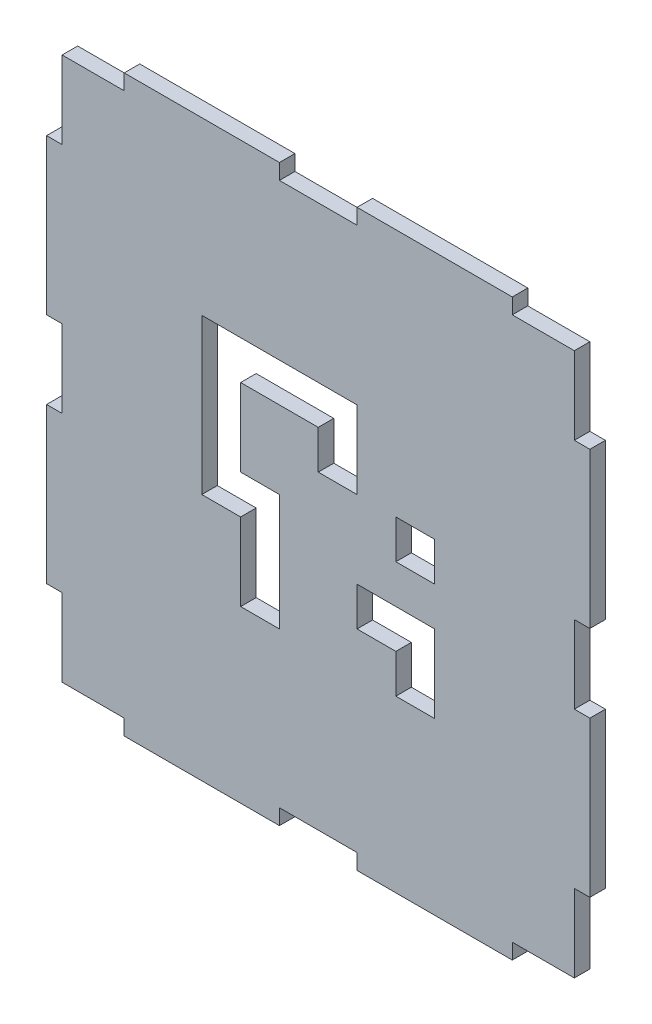
SolidWorks part; units mm, degrees
ref_plane "Front Plane" through (0, 0, 0) normal (0, 0, 1) x (1, 0, 0)
ref_plane "Top Plane" through (0, 0, 0) normal (0, 1, 0) x (1, 0, 0)
ref_plane "Right Plane" through (0, 0, 0) normal (1, 0, 0) x (0, 0, -1)
sketch "Sketch1" plane through (0, 0, 0) normal (0, 0, 1) x (1, 0, 0)
  line L1 (-33, -35) -> (33, -35)
  line L2 (-33, -35) -> (-33, 35)
  line L3 (-33, 35) -> (33, 35)
  line L4 (33, -35) -> (33, 35)
  line L5 (0, 35) -> (0, -35) construction
  line L6 (-33, 0) -> (33, 0) construction
  point P0 (0, 0)
  dimension "D1" = 66
  dimension "D2" = 70
extrude "Boss-Extrude1" add sketch "Sketch1" along normal blind 2
sketch "Sketch2" plane through (0, 0, 0) normal (0, 0, -1) x (-1, 0, 0)
  line L0 (-33, -35) -> (-33, 35) construction
  line L1 (-31, 5) -> (-35, 5)
  line L2 (-31, 5) -> (-31, -5)
  line L3 (-31, -5) -> (-35, -5)
  line L4 (-35, 5) -> (-35, -5)
  line L5 (-33, -5) -> (-33, 5) construction
  line L6 (-31, 0) -> (-35, 0) construction
  line L7 (-33, -35) -> (-33, 0)
  line L8 (-33, -5) -> (-35, -5)
  line L9 (-33, -5) -> (-33, -25)
  line L10 (-33, -25) -> (-35, -25)
  line L11 (-35, -5) -> (-35, -25)
  line L12 (-33, 5) -> (-35, 5)
  line L13 (-33, 5) -> (-33, 25)
  line L14 (-33, 25) -> (-35, 25)
  line L15 (-35, 5) -> (-35, 25)
  line L16 (35, 5) -> (31, 5)
  line L17 (35, 5) -> (35, -5)
  line L18 (35, -5) -> (31, -5)
  line L19 (31, 5) -> (31, -5)
  line L20 (33, -5) -> (33, 5) construction
  line L21 (35, 0) -> (31, 0) construction
  line L22 (33, -35) -> (33, 0)
  line L23 (33, -5) -> (31, -5)
  line L24 (33, -5) -> (33, -25)
  line L25 (33, -25) -> (31, -25)
  line L26 (31, -5) -> (31, -25)
  line L27 (33, 5) -> (31, 5)
  line L28 (33, 5) -> (33, 25)
  line L29 (33, 25) -> (31, 25)
  line L30 (31, 5) -> (31, 25)
  line L32 (33, -5) -> (35, -5)
  line L33 (33, -5) -> (33, -25)
  line L34 (33, -25) -> (35, -25)
  line L35 (35, -5) -> (35, -25)
  line L36 (35, 5) -> (33, 5)
  line L37 (35, 5) -> (35, 25)
  line L38 (35, 25) -> (33, 25)
  line L39 (33, 5) -> (33, 25)
  point P0 (-33, 0)
  point P12 (33, 0)
  line M5 (-33, 35) -> (-33, -35)
  line M7 (33, -35) -> (33, 35)
  dimension "D1" = 4
  dimension "D2" = 10
  dimension "D3" = 20
  dimension "D4" = 20
  dimension "D5" = 4
  dimension "D6" = 10
  dimension "D7" = 20
  dimension "D8" = 20
  dimension "D9" = 35
  dimension "D10" = 35
extrude "Boss-Extrude2" add sketch "Sketch2" against normal blind 2 contours L35 L18 L22 L34 | L37 L38 L16 M7 | L3 L11 L10 M5 | L15 L1 L14 M5
sketch "Sketch3" plane through (0, 0, 0) normal (0, 0, -1) x (-1, 0, 0)
  line L0 (-33, -35) -> (0, -35)
  line L1 (33, -35) -> (-33, -35) construction
  line L2 (-33, 35) -> (0, 35)
  line L3 (-5, -37) -> (5, -37)
  line L4 (-5, -37) -> (-5, -33)
  line L5 (-5, -33) -> (5, -33)
  line L6 (5, -37) -> (5, -33)
  line L7 (0, -33) -> (0, -37) construction
  line L8 (-5, -35) -> (5, -35) construction
  line L9 (5, -35) -> (25, -35)
  line L10 (5, -35) -> (5, -37)
  line L11 (5, -37) -> (25, -37)
  line L12 (25, -35) -> (25, -37)
  line L13 (-5, -35) -> (-25, -35)
  line L14 (-5, -35) -> (-5, -37)
  line L15 (-5, -37) -> (-25, -37)
  line L16 (-25, -35) -> (-25, -37)
  line L17 (-5, 33) -> (5, 33)
  line L18 (-5, 33) -> (-5, 37)
  line L19 (-5, 37) -> (5, 37)
  line L20 (5, 33) -> (5, 37)
  line L21 (0, 37) -> (0, 33) construction
  line L22 (-5, 35) -> (5, 35) construction
  line L23 (5, 35) -> (25, 35)
  line L24 (5, 35) -> (5, 33)
  line L25 (5, 33) -> (25, 33)
  line L26 (25, 35) -> (25, 33)
  line L27 (-5, 35) -> (-25, 35)
  line L28 (-5, 35) -> (-5, 33)
  line L29 (-5, 33) -> (-25, 33)
  line L30 (-25, 35) -> (-25, 33)
  line L32 (-25, 35) -> (-5, 35)
  line L33 (-25, 35) -> (-25, 37)
  line L34 (-25, 37) -> (-5, 37)
  line L35 (-5, 35) -> (-5, 37)
  line L36 (5, 35) -> (25, 35)
  line L37 (5, 35) -> (5, 37)
  line L38 (5, 37) -> (25, 37)
  line L39 (25, 35) -> (25, 37)
  line M6 (-33, -35) -> (33, -35)
  line M16 (33, 35) -> (-33, 35)
  dimension "D1" = 10
  dimension "D2" = 4
  dimension "D3" = 33
  dimension "D4" = 20
  dimension "D5" = 20
  dimension "D6" = 33
  dimension "D7" = 20
  dimension "D8" = 20
extrude "Boss-Extrude3" add sketch "Sketch3" against normal blind 2 contours L34 L33 L2 L18 | L39 L38 L20 M16 | L0 L16 L15 L4 | L12 L6 L11 M6
sketch "Sketch8" plane through (0, 0, 0) normal (0, 0, -1) x (-1, 0, 0)
  line L0 (-15, 19.9491) -> (-15, -20.0509)
  line L1 (-20, -20.0509) -> (20, -20.0509)
  line L2 (-20, -20.0509) -> (-20, 19.9491)
  line L3 (-20, 19.9491) -> (20, 19.9491)
  line L4 (20, -20.0509) -> (20, 19.9491)
  line L5 (0, 19.9491) -> (0, -20.0509) construction
  line L6 (-20, -0.0509) -> (20, -0.0509) construction
  line L7 (-10, 19.9491) -> (-10, -20.0509)
  line L8 (-5, 19.9491) -> (-5, -20.0509)
  line L9 (5, 19.9491) -> (5, -20.0509)
  line L10 (-20, 14.9491) -> (20, 14.9491)
  line L11 (10, 19.9491) -> (10, -20.0509)
  line L12 (15, 19.9491) -> (15, -20.0509)
  line L13 (20, 9.9491) -> (-20, 9.9491)
  line L14 (-20, 4.9491) -> (20, 4.9491)
  line L15 (20, -5.0509) -> (-20, -5.0509)
  line L16 (20, -10.0509) -> (-20, -10.0509)
  line L17 (20, -15.0509) -> (-20, -15.0509)
  line L18 (-20, -0.0509) -> (20, -0.0509)
  line L19 (0, 19.9491) -> (0, -20.0509)
  point P0 (0, -0.0509)
extrude "Cut-Extrude4" cut sketch "Sketch8" against normal blind 10 contours L17 L7 L16 L0 | L16 L7 L15 L0 | L16 L8 L15 L7 | L0 L18 L7 L14 | L19 L13 L8 L14 | L19 L10 L8 L13 | L10 L19 L13 L9 | L13 L11 L10 L9 | L13 L12 L10 L11 | L11 L14 L12 L13 | L11 L18 L12 L14 | L18 L11 L15 L12 | L18 L9 L15 L11 | L16 L11 L15 L9 | L17 L11 L16 L9
